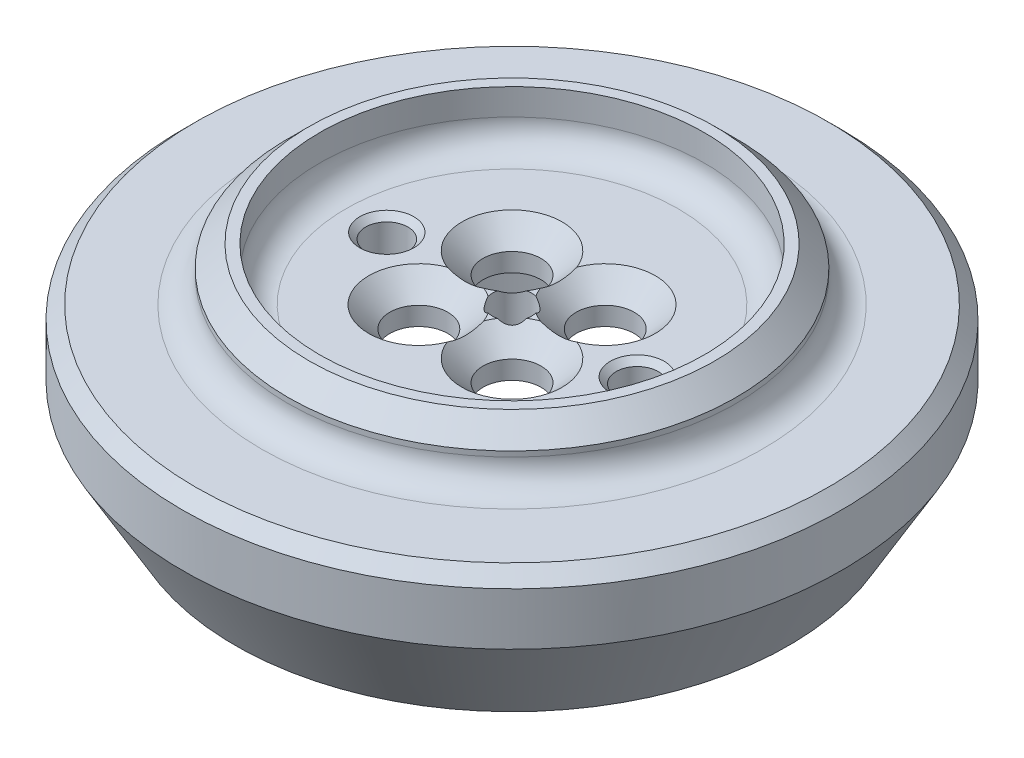
SolidWorks part; units mm, degrees
material "Brass"
ref_plane "Front Plane" through (0, 0, 0) normal (0, 0, 1) x (1, 0, 0)
ref_plane "Top Plane" through (0, 0, 0) normal (0, 1, 0) x (1, 0, 0)
ref_plane "Right Plane" through (0, 0, 0) normal (1, 0, 0) x (0, 0, -1)
sketch "Sketch1" plane through (0, 0, 0) normal (0, 1, 0) x (1, 0, 0)
  circle A0 centre (0, 0) radius 12.5
  dimension "D1" = 25
extrude "Boss-Extrude1" add sketch "Sketch1" along normal blind 1.5
sketch "Sketch2" plane through (0, 1.5, 0) normal (0, 1, 0) x (1, 0, 0)
  circle A0 centre (0, 0) radius 0.75
  dimension "D1" = 1.5
extrude "Cut-Extrude1" cut sketch "Sketch2" against normal through all both and the other way through all
hole_wizard "CSK for M2 Flat Head Machine Screw1" positions "Sketch3" profile "Sketch4" countersink size "M2" standard "ANSI Metric"
sketch "Sketch3" plane through (0, 1.5, 0) normal (0, 1, 0) x (1, 0, 0)
  line L1 (-1.7678, 1.7678) -> (1.7678, 1.7678)
  line L2 (-1.7678, 1.7678) -> (-1.7678, -1.7678)
  line L3 (-1.7678, -1.7678) -> (1.7678, -1.7678)
  line L4 (1.7678, 1.7678) -> (1.7678, -1.7678)
  line L5 (-1.7678, 1.7678) -> (1.7678, -1.7678) construction
  point P0 (-1.7678, 1.7678)
  point P2 (1.7678, 1.7678)
  point P4 (1.7678, -1.7678)
  point P6 (-1.7678, -1.7678)
  point P120 (0, 0)
  dimension "D1" = 5
sketch "Sketch4" plane through (-1.7678, 1.5, -1.7678) normal (1, 0, 0) x (0, 0, 1)
  line L0 (0, 0) -> (0, 5.6609)
  line L1 (0, 5.6609) -> (1.1, 5)
  line L2 (1.1, 5) -> (1.1, 0.8)
  line L3 (1.1, 0.8) -> (1.9, 0)
  line L5 (1.9, 0) -> (0, 0)
  line L6 (-1.1, 0.8) -> (-1.9, 0) construction
  line L10 (0, 5.6609) -> (-1.1, 5) construction
  line L11 (0, -6.35) -> (0, 107.95) construction
  dimension "Hole Dia." = 2.2
  dimension "Hole Depth" = 5
  dimension "Near C'Sink Dia." = 3.8
  dimension "Near C'Sink Angle" = 90
  dimension "Drill Angle" = 118
sketch "Sketch6" plane through (0, 0, 0) normal (0, 0, 1) x (1, 0, 0)
  line L0 (-12.5, 0) -> (-12.5, -1.15)
  line L1 (-12.5, -1.15) -> (-7.05, -1.15)
  line L2 (-7.05, -1.15) -> (-5, 0)
  line L3 (-5, 0) -> (-12.5, 0)
  line L4 (0, 0) -> (0, -5.6432) construction
  dimension "D1" = 1.15
  dimension "D2" = 5
  dimension "D3" = 7.05
revolve "Revolve1" add sketch "Sketch6" angle 360 about L4
sketch "Sketch7" plane through (0, -1.15, 0) normal (0, -1, 0) x (1, 0, 0)
  circle A0 centre (0, 0) radius 7.05 construction
  circle A1 centre (0, 0) radius 12.5
  circle A2 centre (0, 0) radius 12.5
  circle A3 centre (0, 0) radius 7.05
  dimension "D1" = 0
extrude "Boss-Extrude2" add sketch "Sketch7" along normal blind 3.3
sketch "Sketch11" plane through (0, 1.5, 0) normal (0, 1, 0) x (1, 0, 0)
  line L0 (0, 0) -> (-3.2481, 0) construction
  line L1 (-7.25, 5.1678) -> (-7.25, -5.1678)
  line L2 (-7.25, -5.1678) -> (7.25, -5.1678)
  line L3 (7.25, -5.1678) -> (7.25, 5.1678)
  line L4 (7.25, 5.1678) -> (-7.25, 5.1678)
  line L5 (-7.25, 5.1678) -> (7.25, -5.1678) construction
  line L6 (-1.7678, -3.6678) -> (-1.7678, -5.1678) construction
  line L7 (-0.6889, -3.6678) -> (-2.8466, -3.6678) construction
  circle A0 centre (0, 0) radius 10
  arc A4 (-2.4642, 0) -> (0, -2.4642) centre (-1.7678, -1.7678) ccw construction
  dimension "D1" = 1.5
  dimension "D3" = 20
  dimension "D2" = 14.5
extrude "Boss-Extrude3" [suppressed] add sketch "Sketch11" along normal blind 3
fillet "Fillet2" [suppressed] radius 5
fillet "Fillet3" [suppressed] radius 1
sketch "Sketch15" plane through (0, 1.5, 0) normal (0, 1, 0) x (1, 0, 0)
  circle A0 centre (0, 0) radius 7.3
  circle A1 centre (0, 0) radius 8.5
  dimension "D1" = 14.6
  dimension "D2" = 17
extrude "Boss-Extrude4" add sketch "Sketch15" along normal blind 2
fillet "Fillet1" radius 1 4 edges at (0, 0, 5) (0, -1.15, 7.05) (0, 1.5, 7.3) (0, 1.5, 8.5)
loft "Loft2" [suppressed] add
sketch "Sketch14" [suppressed] plane through (0, 4.5, 0) normal (0, 1, 0) x (1, 0, 0)
  circle A0 centre (0, 0) radius 10 construction
  circle A1 centre (0, 0) radius 10
extrude "Cut-Extrude2" [suppressed] cut sketch "Sketch14" against normal through all both and the other way through all
combine bodies "Combine1" [suppressed] operation type add bodies to combine 110 107
chamfer "Chamfer1" distance 0.5 angle 45 1 edges at (0, 1.5, 12.5)
chamfer "Chamfer2" distance 1 angle 45 1 edges at (0, -4.45, -7.05)
chamfer "Chamfer3" distance 2 angle 60 1 edges at (0, -4.45, -12.5)
hole_wizard "M2x0.4 Tapped Hole1" positions "Sketch8" profile "Sketch9" tap size "M2x0.4" standard "ANSI Metric"
sketch "Sketch8" plane through (0, 1.5, 0) normal (0, 1, 0) x (1, 0, 0)
  line L0 (-4.75, 0) -> (4.75, 0) construction
  point P0 (-4.75, 0)
  point P2 (4.75, 0)
  dimension "D1" = 9.5
sketch "Sketch9" plane through (-4.75, 1.5, 0) normal (1, 0, 0) x (0, 0, 1)
  line L0 (0, 0) -> (0, 5.6807)
  line L1 (0, 5.6807) -> (0.8, 5.2)
  line L2 (0.8, 5.2) -> (0.8, 0.225)
  line L3 (0.8, 0.225) -> (1.025, 0)
  line L5 (1.025, 0) -> (0, 0)
  line L6 (-0.8, 0.225) -> (-1.025, 0) construction
  line L10 (0, 5.6807) -> (-0.8, 5.2) construction
  line L11 (0, -6.35) -> (0, 107.95) construction
  dimension "Tap Drill Dia." = 1.6
  dimension "Tap Drill Depth" = 5.2
  dimension "Near C'Sink Dia." = 2.05
  dimension "Near C'Sink Angle" = 90
  dimension "Drill Angle" = 118
cosmetic thread "Hole Thread1" parameters "D1"=2.4801, "D2"=2
cosmetic thread "Hole Thread2" parameters "D1"=2.4801, "D2"=2
chamfer "Chamfer4" distance 0.8 angle 45 1 edges at (0, 3.5, 8.5)
